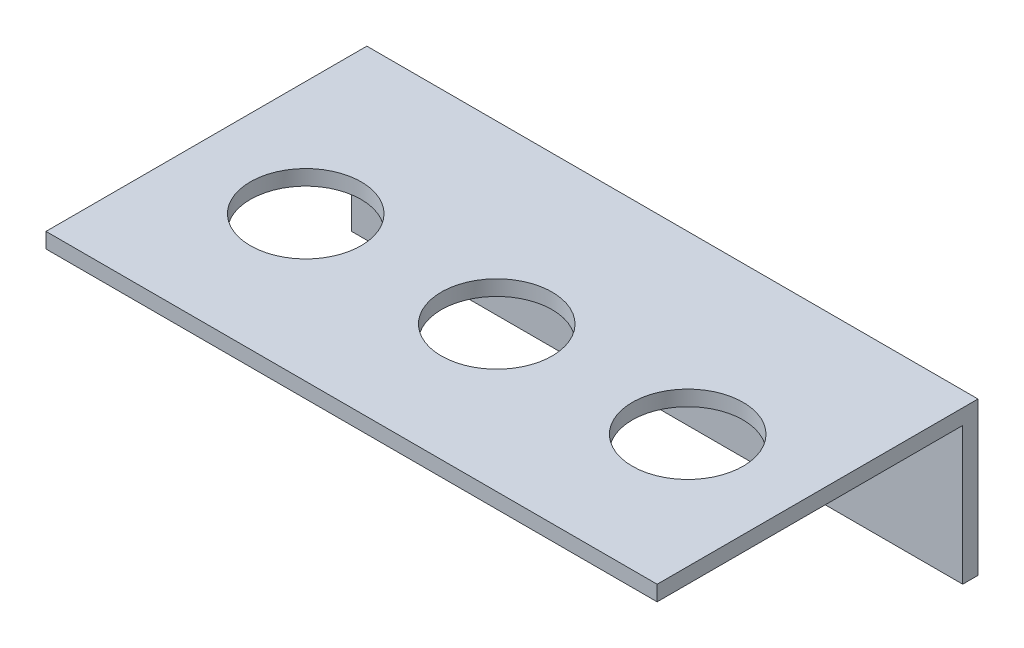
SolidWorks part; units mm, degrees
ref_plane "Ön Düzlem" through (0, 0, 0) normal (0, 0, 1) x (1, 0, 0)
ref_plane "Üst Düzlem" through (0, 0, 0) normal (0, 1, 0) x (1, 0, 0)
ref_plane "Sağ Düzlem" through (0, 0, 0) normal (1, 0, 0) x (0, 0, -1)
sketch "Çizim1" plane through (0, 0, 0) normal (0, 0, 1) x (1, 0, 0)
  line L1 (-40, 10) -> (40, 10)
  line L2 (-40, 10) -> (-40, -10)
  line L3 (-40, -10) -> (40, -10)
  line L4 (40, 10) -> (40, -10)
  line L5 (-40, 10) -> (40, -10) construction
  line L6 (-40, -10) -> (40, 10) construction
  point P0 (0, 0)
  dimension "D1" = 20
  dimension "D2" = 80
extrude "Yükseklik-Ekstrüzyon1" add sketch "Çizim1" along normal blind 42
shell "İç Boşaltma1" thickness 2
sketch "Çizim2" plane through (0, 10, 0) normal (0, 1, 0) x (1, 0, 0)
  circle A0 centre (0, -23) radius 7.25
  circle A1 centre (-25, -23) radius 7.25
  circle A2 centre (25, -23) radius 7.25
  dimension "D1" = 14.5
  dimension "D4" = 25
  dimension "D5" = 25
  dimension "D6" = 23
extrude "Kes-Ekstrüzyon1" cut sketch "Çizim2" against normal blind 42
